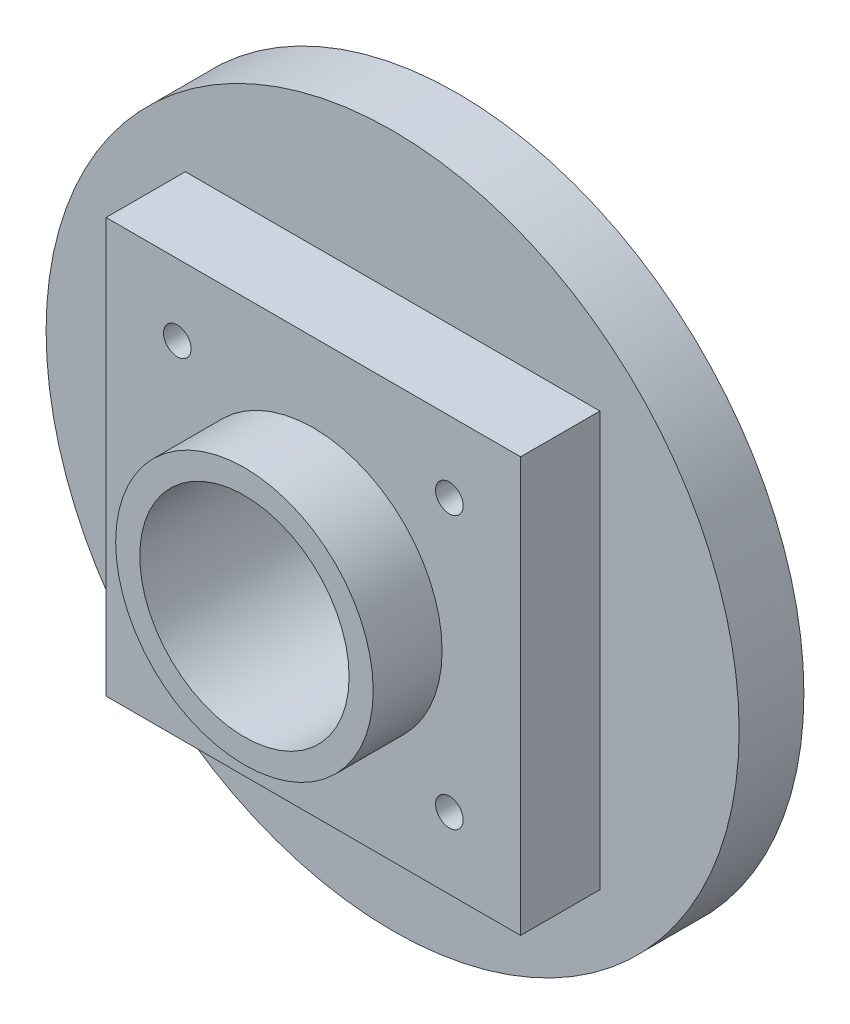
SolidWorks part; units mm, degrees
ref_plane "Front Plane" through (0, 0, 0) normal (0, 0, 1) x (1, 0, 0)
ref_plane "Top Plane" through (0, 0, 0) normal (0, 1, 0) x (1, 0, 0)
ref_plane "Right Plane" through (0, 0, 0) normal (1, 0, 0) x (0, 0, -1)
sketch "Sketch1" plane through (0, 0, 0) normal (0, 0, 1) x (1, 0, 0)
  circle A0 centre (0, 0) radius 33.9725
  dimension "D1" = 67.945
extrude "Boss-Extrude2" add sketch "Sketch1" along normal blind 6.35
sketch "Sketch2" plane through (0, 0, 0) normal (0, 0, -1) x (-1, 0, 0)
  circle A0 centre (0, 0) radius 17.145
  dimension "D1" = 34.29
extrude "Boss-Extrude3" add sketch "Sketch2" along normal blind 6.985
sketch "Sketch3" plane through (0, 0, 6.35) normal (0, 0, 1) x (1, 0, 0)
  line L0 (0, 17.876) -> (0, -23.4773) construction
  line L1 (-20.32, 20.32) -> (20.32, 20.32)
  line L2 (-20.32, 20.32) -> (-20.32, -20.32)
  line L3 (-20.32, -20.32) -> (20.32, -20.32)
  line L4 (20.32, 20.32) -> (20.32, -20.32)
  line L5 (-21.0511, 0) -> (17.901, 0) construction
  dimension "D1" = 40.64
  dimension "D2" = 40.64
extrude "Boss-Extrude4" add sketch "Sketch3" along normal blind 7.7724
sketch "Sketch4" plane through (0, 0, 14.1224) normal (0, 0, 1) x (1, 0, 0)
  circle A0 centre (0, 0) radius 10.2616
  dimension "D1" = 20.5232
extrude "Cut-Extrude1" cut sketch "Sketch4" against normal through all
hole_wizard "#6-32 Tapped Hole1" positions "Sketch7" profile "Sketch6" tap size "#6-32" standard "ANSI Inch"
sketch "Sketch7" plane through (0, 0, 14.1224) normal (0, 0, 1) x (1, 0, 0)
  point P0 (-13.335, 13.335)
  point P2 (13.335, 13.335)
  point P4 (13.335, -13.335)
  point P6 (-13.335, -13.335)
  dimension "D1" = 13.335
  dimension "D2" = 13.335
  dimension "D3" = 13.335
  dimension "D4" = 13.335
sketch "Sketch6" plane through (-13.335, 13.335, 14.1224) normal (1, 0, 0) x (0, -1, 0)
  line L0 (0, 0) -> (0, 10.2107)
  line L1 (0, 10.2107) -> (1.3525, 9.398)
  line L2 (1.3525, 9.398) -> (1.3525, 0)
  line L5 (1.3525, 0) -> (0, 0)
  line L10 (0, 10.2107) -> (-1.3525, 9.398) construction
  line L11 (0, -6.35) -> (0, 107.95) construction
  dimension "Tap Drill Dia." = 2.7051
  dimension "Tap Drill Depth" = 9.398
  dimension "Drill Angle" = 118
cosmetic thread "Hole Thread1" parameters "D1"=7.112, "D2"=3.5052
cosmetic thread "Hole Thread2" parameters "D1"=7.112, "D2"=3.5052
cosmetic thread "Hole Thread3" parameters "D1"=7.112, "D2"=3.5052
cosmetic thread "Hole Thread4" parameters "D1"=7.112, "D2"=3.5052
sketch "Sketch8" plane through (0, 0, 14.1224) normal (0, 0, 1) x (1, 0, 0)
  circle A0 centre (0, 0) radius 12.6238
  circle A1 centre (0, 0) radius 10.2616
  circle A2 centre (0, 0) radius 10.2616 construction
  dimension "D1" = 25.2476
extrude "Boss-Extrude5" add sketch "Sketch8" along normal blind 6.7564
